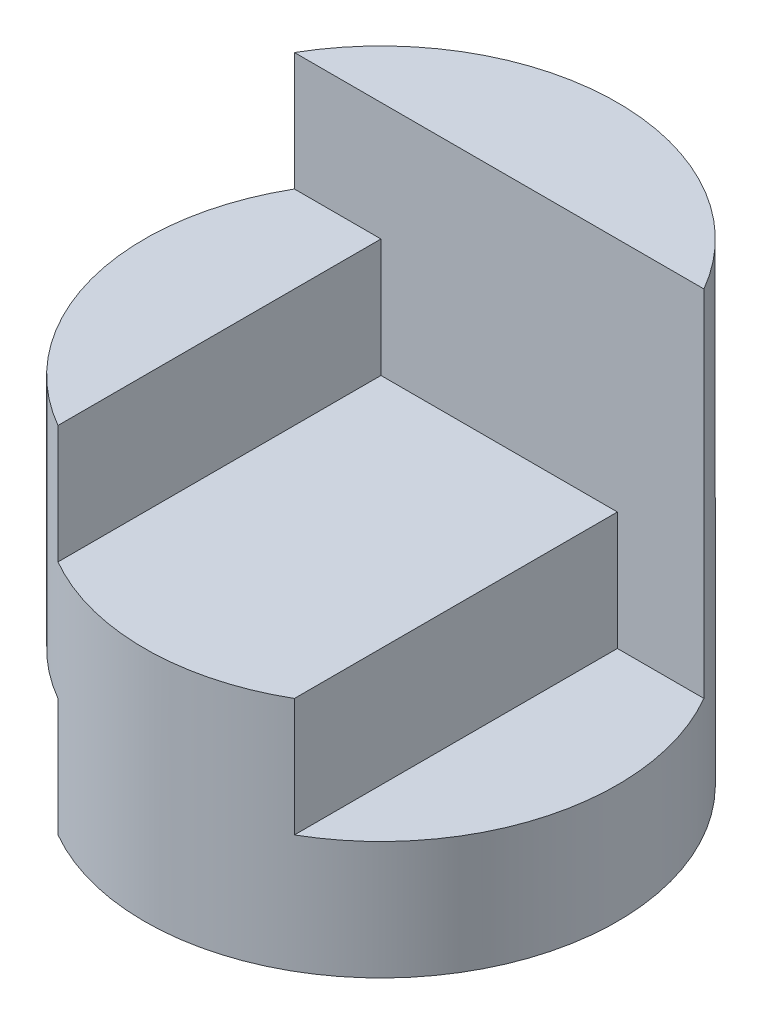
SolidWorks part; units mm, degrees
ref_plane "Front" through (0, 0, 0) normal (0, 0, 1) x (1, 0, 0)
ref_plane "Top" through (0, 0, 0) normal (0, 1, 0) x (1, 0, 0)
ref_plane "Right" through (0, 0, 0) normal (1, 0, 0) x (0, 0, -1)
sketch "Sketch1" plane through (0, 0, 0) normal (0, 1, 0) x (1, 0, 0)
  circle A0 centre (0, 0) radius 2
  dimension "D1" = 4
extrude "Boss-Extrude1" add sketch "Sketch1" along normal blind 4
sketch "Sketch2" plane through (0, 0, 0) normal (0, 0, 1) x (1, 0, 0)
  line L0 (-2, 4) -> (2, 4)
  line L1 (2, 4) -> (2, 1)
  line L2 (2, 0) -> (2, 4) construction
  line L3 (2, 1) -> (1, 1)
  line L4 (1, 1) -> (1, 2)
  line L5 (1, 2) -> (-1, 2)
  line L6 (-1, 2) -> (-1, 3)
  line L7 (-1, 3) -> (-2, 3)
  line L8 (-2, 3) -> (-2, 4)
  line L10 (-2, 0) -> (-1, 0)
  line L11 (-2, 0) -> (-2, 1)
  line L12 (-2, 1) -> (-1, 1)
  line L13 (-1, 0) -> (-1, 1)
  dimension "D1" = 1
  dimension "D2" = 3
  dimension "D3" = 1
  dimension "D4" = 1
  dimension "D5" = 1
extrude "Cut-Extrude1" cut sketch "Sketch2" against normal blind 1 and the other way blind 3
